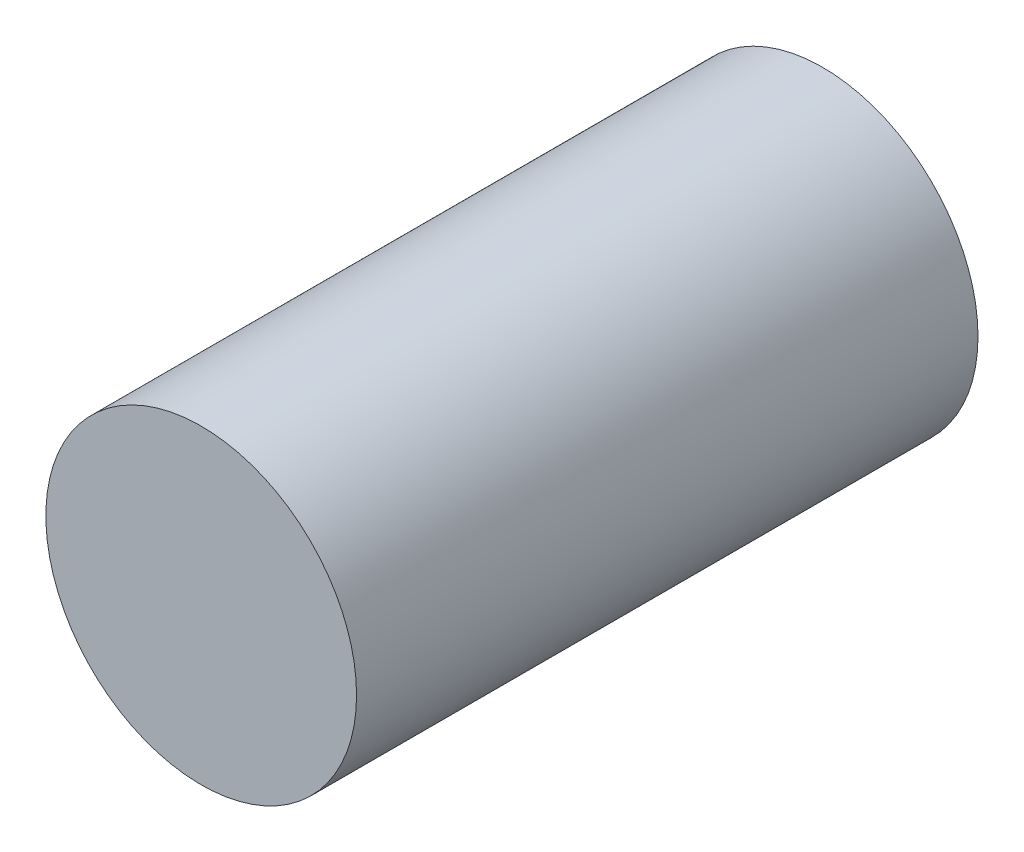
SolidWorks part; units mm, degrees
ref_plane "Front" through (0, 0, 0) normal (0, 0, 1) x (1, 0, 0)
ref_plane "Top" through (0, 0, 0) normal (0, 1, 0) x (1, 0, 0)
ref_plane "Right" through (0, 0, 0) normal (1, 0, 0) x (0, 0, -1)
sketch "Sketch1" plane through (0, 0, 0) normal (0, 0, 1) x (1, 0, 0)
  circle A0 centre (0, 0) radius 25.4
  dimension "D1" = 50.8
extrude "Boss-Extrude1" add sketch "Sketch1" along normal blind 101.6
